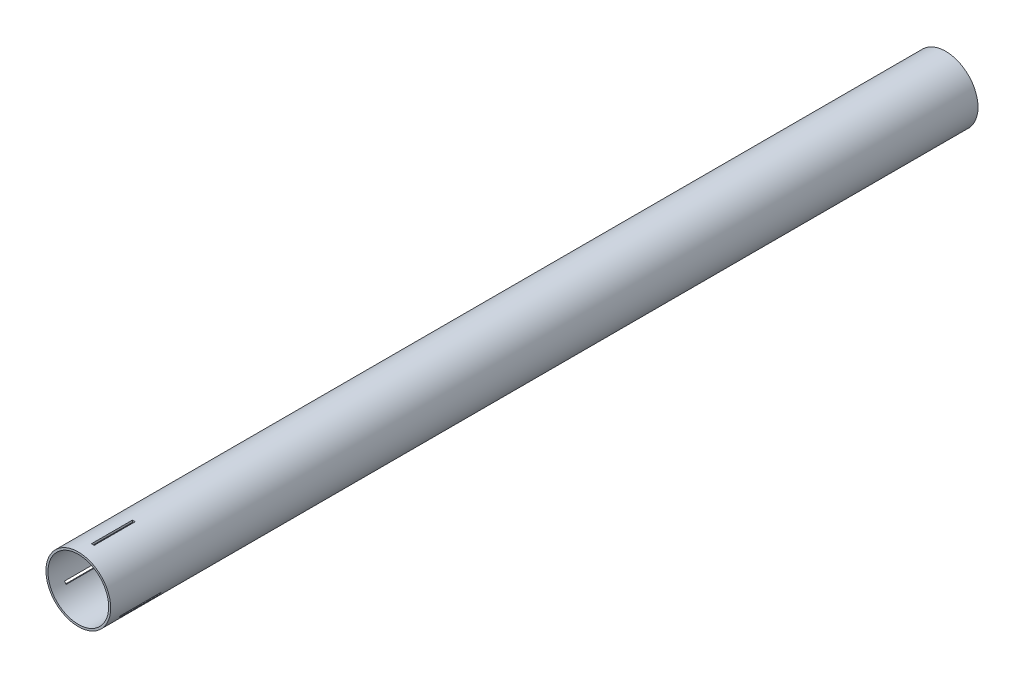
SolidWorks part; units mm, degrees
ref_plane "Front Plane" through (0, 0, 0) normal (0, 0, 1) x (1, 0, 0)
ref_plane "Top Plane" through (0, 0, 0) normal (0, 1, 0) x (1, 0, 0)
ref_plane "Right Plane" through (0, 0, 0) normal (1, 0, 0) x (0, 0, -1)
sketch "Sketch1" plane through (0, 0, 0) normal (0, 0, 1) x (1, 0, 0)
  circle A0 centre (0, 0) radius 23.6982
  circle A1 centre (0, 0) radius 22.225
  dimension "D1" = 47.3964
  dimension "D2" = 44.45
extrude "Boss-Extrude1" add sketch "Sketch1" along normal blind 635
ref_plane "Plane1" through (0, 100, 0) normal (0, 1, 0) x (1, 0, 0)
sketch "Sketch2" plane through (0, 100, 0) normal (0, 1, 0) x (1, 0, 0)
  line L0 (-23.6982, -635) -> (23.6982, -635) construction
  line L3 (1.5875, -625) -> (1.5875, -595)
  line L4 (-0.4125, -625) -> (-0.4125, -595)
  line L5 (-0.4125, -595) -> (1.5875, -595)
  line L6 (-0.4125, -625) -> (1.5875, -625)
  dimension "D1" = 10
  dimension "D2" = 30
  dimension "D3" = 2
extrude "Cut-Extrude1" cut sketch "Sketch2" against normal up to next
pattern_circular "CirPattern2" count 3 over 360 about axis through (0, 0, 0) along (0, 0, 1) of "Cut-Extrude1"
